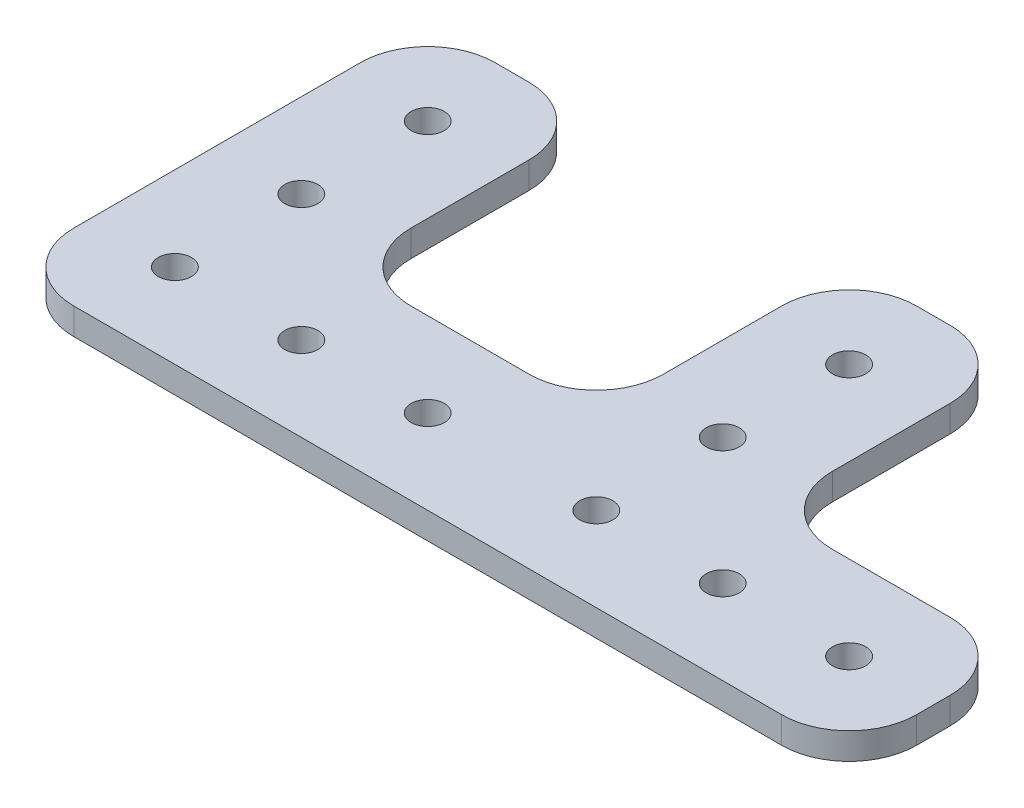
SolidWorks part; units mm, degrees
material "ABS"
ref_plane "Front Plane" through (0, 0, 0) normal (0, 0, 1) x (1, 0, 0)
ref_plane "Top Plane" through (0, 0, 0) normal (0, 1, 0) x (1, 0, 0)
ref_plane "Right Plane" through (0, 0, 0) normal (1, 0, 0) x (0, 0, -1)
sketch "Sketch1" plane through (0, 25.4, 0) normal (0, 1, 0) x (1, 0, 0)
  line L0 (-165.1, 152.4) -> (-190.5, 152.4) construction
  line L1 (-190.5, 152.4) -> (-190.5, -279.4) construction
  line L3 (-165.1, -279.4) -> (-165.1, 152.4) construction
  line L4 (-101.6, 152.4) -> (-127, 152.4) construction
  line L5 (-127, 152.4) -> (-127, -279.4) construction
  line L7 (-101.6, -279.4) -> (-101.6, 152.4) construction
  line L8 (-190.5, -279.4) -> (-190.5, -304.8) construction
  line L9 (-190.5, -304.8) -> (190.5, -304.8) construction
  line L10 (190.5, -304.8) -> (190.5, -279.4) construction
  line L11 (190.5, -279.4) -> (-190.5, -279.4) construction
  line L12 (-165.1, 152.4) -> (-190.5, 152.4)
  line L13 (-190.5, -241.3) -> (-190.5, -279.4)
  line L14 (-165.1, -241.3) -> (-190.5, -241.3)
  line L15 (-165.1, -279.4) -> (-165.1, -241.3)
  line L16 (-101.6, 152.4) -> (-127, 152.4)
  line L17 (-127, -241.3) -> (-127, -279.4)
  line L18 (-63.5, -292.1) -> (-190.5, -292.1) construction
  line L19 (-101.6, -279.4) -> (-101.6, -241.3)
  line L20 (-190.5, -279.4) -> (-190.5, -304.8)
  line L21 (-190.5, -304.8) -> (-63.5, -304.8)
  line L22 (190.5, -304.8) -> (190.5, -279.4)
  line L23 (-63.5, -279.4) -> (-101.6, -279.4)
  line L24 (-63.5, -304.8) -> (-63.5, -279.4)
  line L25 (-101.6, -241.3) -> (-127, -241.3)
  line L26 (-127, -279.4) -> (-165.1, -279.4)
  line L27 (-177.8, -241.3) -> (-177.8, -304.8) construction
  line L28 (-114.3, -241.3) -> (-114.3, -304.8) construction
  circle A0 centre (-114.3, -292.1) radius 2.5
  circle A1 centre (-177.8, -292.1) radius 2.5
  circle A2 centre (-158.75, -292.1) radius 2.5
  circle A3 centre (-95.25, -292.1) radius 2.5
  circle A4 centre (-139.7, -292.1) radius 2.5
  circle A5 centre (-76.2, -292.1) radius 2.5
  circle A6 centre (-114.3, -273.05) radius 2.5
  circle A7 centre (-177.8, -273.05) radius 2.5
  circle A8 centre (-114.3, -254) radius 2.5
  circle A9 centre (-177.8, -254) radius 2.5
  line M3 (-190.5, -279.4) -> (-190.5, -304.8)
  line M4 (-190.5, -304.8) -> (190.5, -304.8)
  line M6 (190.5, -279.4) -> (-190.5, -279.4)
  dimension "D3" = 5
  dimension "D1" = 127
  dimension "D2" = 63.5
  dimension "D4" = 3
  dimension "D5" = 3
extrude "Boss-Extrude1" add sketch "Sketch1" along normal blind 4 contours L24 A5 A4 A3 A2 A1 A0 M4 M6 M3 | L19 L25 L17 A8 A6 M6 | L15 L14 L13 A9 A7 M6
fillet "Fillet1" radius 10.16 10 edges at (-190.5, 27.4, 241.3) (-165.1, 27.4, 241.3) (-127, 27.4, 241.3) (-101.6, 27.4, 241.3) (-63.5, 27.4, 279.4) (-63.5, 27.4, 304.8) (-190.5, 27.4, 304.8) (-101.6, 27.4, 279.4) (-165.1, 27.4, 279.4) (-127, 27.4, 279.4)
